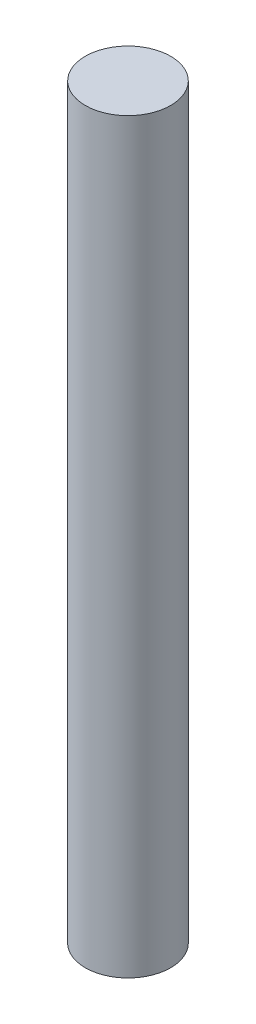
SolidWorks part; units mm, degrees
ref_plane "Front Plane" through (0, 0, 0) normal (0, 0, 1) x (1, 0, 0)
ref_plane "Top Plane" through (0, 0, 0) normal (0, 1, 0) x (1, 0, 0)
ref_plane "Right Plane" through (0, 0, 0) normal (1, 0, 0) x (0, 0, -1)
sketch "Sketch1" plane through (0, 0, 0) normal (0, 1, 0) x (1, 0, 0)
  circle A0 centre (0, 0) radius 4
  dimension "D1" = 8
extrude "Boss-Extrude1" add sketch "Sketch1" along normal blind 70
